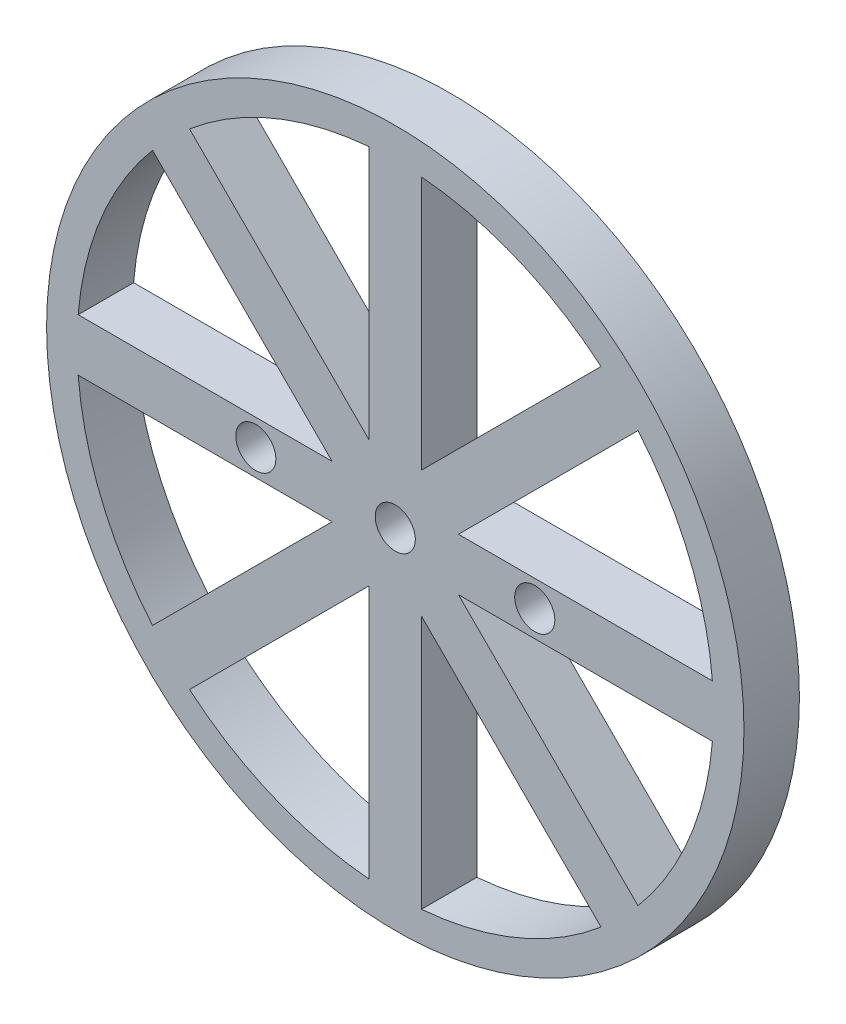
SolidWorks part; units mm, degrees
ref_plane "Front Plane" through (0, 0, 0) normal (0, 0, 1) x (1, 0, 0)
ref_plane "Top Plane" through (0, 0, 0) normal (0, 1, 0) x (1, 0, 0)
ref_plane "Right Plane" through (0, 0, 0) normal (1, 0, 0) x (0, 0, -1)
sketch "Sketch1" plane through (0, 0, 0) normal (0, 0, 1) x (1, 0, 0)
  line L0 (-1020, 0) -> (-20, 0) construction
  line L1 (0, -1036.5) -> (0, -20) construction
  line L2 (-1.5, 18.1883) -> (-1.5, 3.6213)
  line L3 (-1.5, -3.6213) -> (-1.5, -18.1883)
  line L4 (1.5, -3.6213) -> (1.5, -18.1883)
  line L5 (1.5, 18.1883) -> (1.5, 3.6213)
  line L6 (-18.1883, 1.5) -> (-3.6213, 1.5)
  line L7 (-18.1883, -1.5) -> (-3.6213, -1.5)
  line L8 (3.6213, 1.5) -> (18.1883, 1.5)
  line L9 (3.6213, -1.5) -> (18.1883, -1.5)
  line L10 (-707.1068, 707.1068) -> (-14.1421, 14.1421) construction
  line L11 (-11.8004, 13.9217) -> (-1.5, 3.6213)
  line L12 (-13.9217, 11.8004) -> (-3.6213, 1.5)
  line L13 (1.5, -3.6213) -> (11.8004, -13.9217)
  line L14 (3.6213, -1.5) -> (13.9217, -11.8004)
  line L15 (-1.5, -3.6213) -> (-11.8004, -13.9217)
  line L16 (-3.6213, -1.5) -> (-13.9217, -11.8004)
  line L17 (11.8004, 13.9217) -> (1.5, 3.6213)
  line L18 (13.9217, 11.8004) -> (3.6213, 1.5)
  line L20 (20, 0) -> (1020, 0) construction
  line L22 (14.1421, -14.1421) -> (720.0115, -720.0115) construction
  line L23 (0, 20) -> (0, 1020) construction
  circle A0 centre (0, 0) radius 20
  arc A1 (-13.9217, 11.8004) -> (-18.1883, 1.5) centre (0, 0) ccw
  circle A2 centre (0, 0) radius 1.15
  arc A4 (-1.5, 18.1883) -> (-11.8004, 13.9217) centre (0, 0) ccw
  arc A5 (11.8004, 13.9217) -> (1.5, 18.1883) centre (0, 0) ccw
  arc A6 (18.1883, 1.5) -> (13.9217, 11.8004) centre (0, 0) ccw
  arc A7 (13.9217, -11.8004) -> (18.1883, -1.5) centre (0, 0) ccw
  arc A8 (1.5, -18.1883) -> (11.8004, -13.9217) centre (0, 0) ccw
  arc A9 (-11.8004, -13.9217) -> (-1.5, -18.1883) centre (0, 0) ccw
  arc A10 (-18.1883, -1.5) -> (-13.9217, -11.8004) centre (0, 0) ccw
  circle A11 centre (-8, 0) radius 1.15
  circle A12 centre (8, 0) radius 1.15
  point P9 (0, 0)
  point P10 (-1.5, 19.9437)
  point P11 (-1.5, -19.9437)
  point P21 (-18.1883, 1.5)
  point P22 (18.1883, 1.5)
  point P32 (-11.8004, 13.9217)
  point P34 (13.9217, -11.8004)
  dimension "D1" = 40
  dimension "D2" = 10.3004
  dimension "D3" = 2.3
  dimension "D4" = 2.3
  dimension "D20" = 2.3
  dimension "D5" = 1.5
  dimension "D6" = 1.5
  dimension "D7" = 1.5
  dimension "D8" = 1.5
  dimension "D9" = 36.3765
  dimension "D10" = 1.5
  dimension "D11" = 45
  dimension "D12" = 1.5
  dimension "D13" = 1.5
  dimension "D14" = 45
  dimension "D15" = 45
  dimension "D16" = 45
  dimension "D17" = 45
  dimension "D18" = 45
  dimension "D19" = 8
  dimension "D21" = 8
  dimension "D22" = 1.5
  dimension "D23" = 1.5
extrude "Boss-Extrude1" add sketch "Sketch1" along normal blind 3.18
